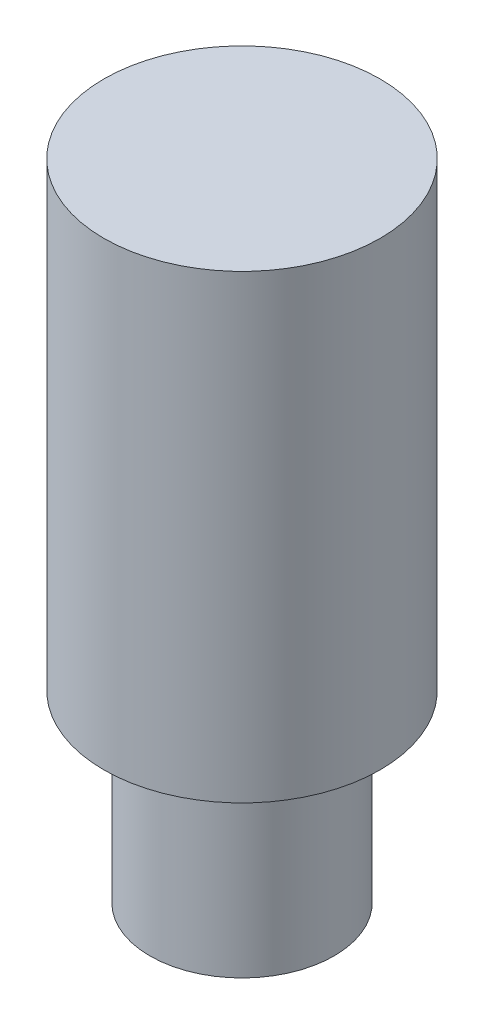
SolidWorks part; units mm, degrees
ref_plane "Ebene vorne" through (0, 0, 0) normal (0, 0, 1) x (1, 0, 0)
ref_plane "Ebene oben" through (0, 0, 0) normal (0, 1, 0) x (1, 0, 0)
ref_plane "Ebene rechts" through (0, 0, 0) normal (1, 0, 0) x (0, 0, -1)
sketch "Skizze1" plane through (0, 0, 0) normal (0, 1, 0) x (1, 0, 0)
  circle A0 centre (0, 0) radius 1
extrude "Aufsatz-Linear austragen1" add sketch "Skizze1" along normal blind 2
sketch "Skizze2" plane through (0, 2, 0) normal (0, 1, 0) x (1, 0, 0)
  circle A0 centre (0, 0) radius 1.5
extrude "Aufsatz-Linear austragen2" add sketch "Skizze2" along normal blind 5
